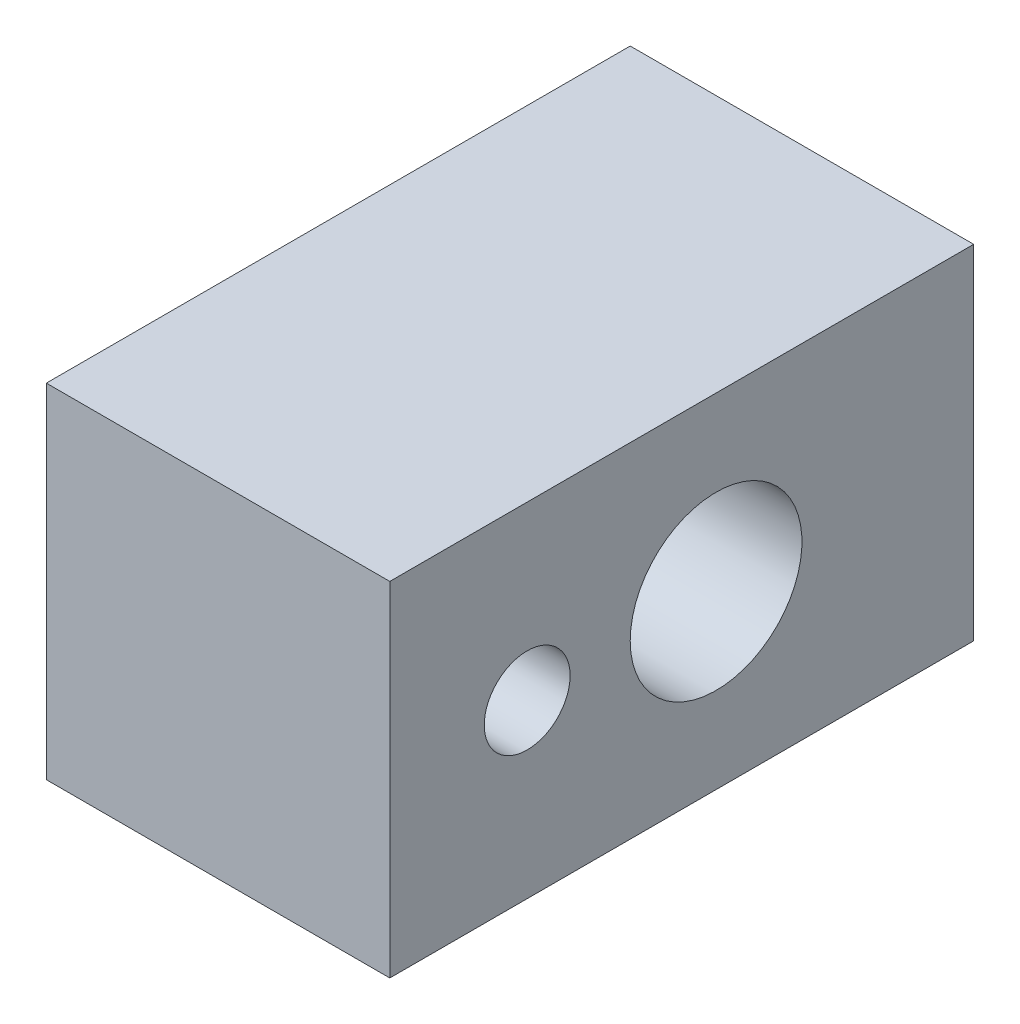
SolidWorks part; units mm, degrees
ref_plane "Plan de face" through (0, 0, 0) normal (0, 0, 1) x (1, 0, 0)
ref_plane "Plan de dessus" through (0, 0, 0) normal (0, 1, 0) x (1, 0, 0)
ref_plane "Plan de droite" through (0, 0, 0) normal (1, 0, 0) x (0, 0, -1)
sketch "Esquisse1" plane through (0, 0, 0) normal (0, 0, 1) x (1, 0, 0)
  line L1 (0, 0) -> (-10, 0)
  line L2 (0, 0) -> (0, 10)
  line L3 (0, 10) -> (-10, 10)
  line L4 (-10, 0) -> (-10, 10)
  dimension "D1" = 10
  dimension "D2" = 10
extrude "Extrusion1" add sketch "Esquisse1" along normal blind 17
sketch "Esquisse2" plane through (0, 0, 0) normal (1, 0, 0) x (0, 0, -1)
  line L0 (0, 5) -> (-7.5, 5)
  line L1 (0, 0) -> (0, 10) construction
  circle A0 centre (-7.5, 5) radius 2.5
  dimension "D2" = 5
  dimension "D1" = 7.5
extrude "Enlèv. mat.-Extru.1" cut sketch "Esquisse2" against normal through all
hole_wizard "Trou taraudé M3x0.51" positions "Esquisse3D1" profile "Esquisse3" tap size "M3x0.5" standard "ISO" end condition through all
sketch3d "Esquisse3D1"
  line L0 (0, 5, 13) -> (0, 5, 17)
  line L1 (0, 0, 17) -> (0, 10, 17) construction
  circle A0 centre (0, 5, 7.5) radius 2.5 construction
  point P0 (0, 5, 13)
  point P5 (-2.5, 5, 7.5)
  dimension "D1" = 5.5
sketch "Esquisse3" plane through (0, 5, 13) normal (0, 1, 0) x (0, 0, -1)
  line L0 (0, 0) -> (0, 10)
  line L1 (0, 10) -> (1.25, 10)
  line L2 (1.25, 10) -> (1.25, 0)
  line L5 (1.25, 0) -> (0, 0)
  line L11 (0, -6.35) -> (0, 107.95) construction
  dimension "Diamètre du trou pour taraudage jusqu'au prochain" = 2.5
  dimension "Profondeur du trou pour taraudage jusqu'au prochain" = 10
cosmetic thread "Filetage de perçage1" parameters "D2"=3
hole_wizard "Trou taraudé M4x0.71" positions "Esquisse3D2" profile "Esquisse4" tap size "M4x0.7" standard "ISO"
sketch3d "Esquisse3D2"
  line L8 (-10, 10, 0) -> (-10, 0, 0) construction
  line L9 (-10, 0, 0) -> (0, 0, 0) construction
  point P22 (-5, 5, 0)
  dimension "D1" = 5
  dimension "D2" = 5
cosmetic thread "Filetage de perçage2" parameters "D1"=5.6218, "D2"=4
sketch "Esquisse4" plane through (-5, 5, 0) normal (1, 0, 0) x (0, 1, 0)
  line L0 (0, 0) -> (0, 8.9914)
  line L1 (0, 8.9914) -> (1.65, 8)
  line L2 (1.65, 8) -> (1.65, 0)
  line L5 (1.65, 0) -> (0, 0)
  line L10 (0, 8.9914) -> (-1.65, 8) construction
  line L11 (0, -6.35) -> (0, 107.95) construction
  dimension "Diamètre du trou pour taraudage" = 3.3
  dimension "Profondeur du trou pour taraudage" = 8
  dimension "Angle de pointe" = 118
